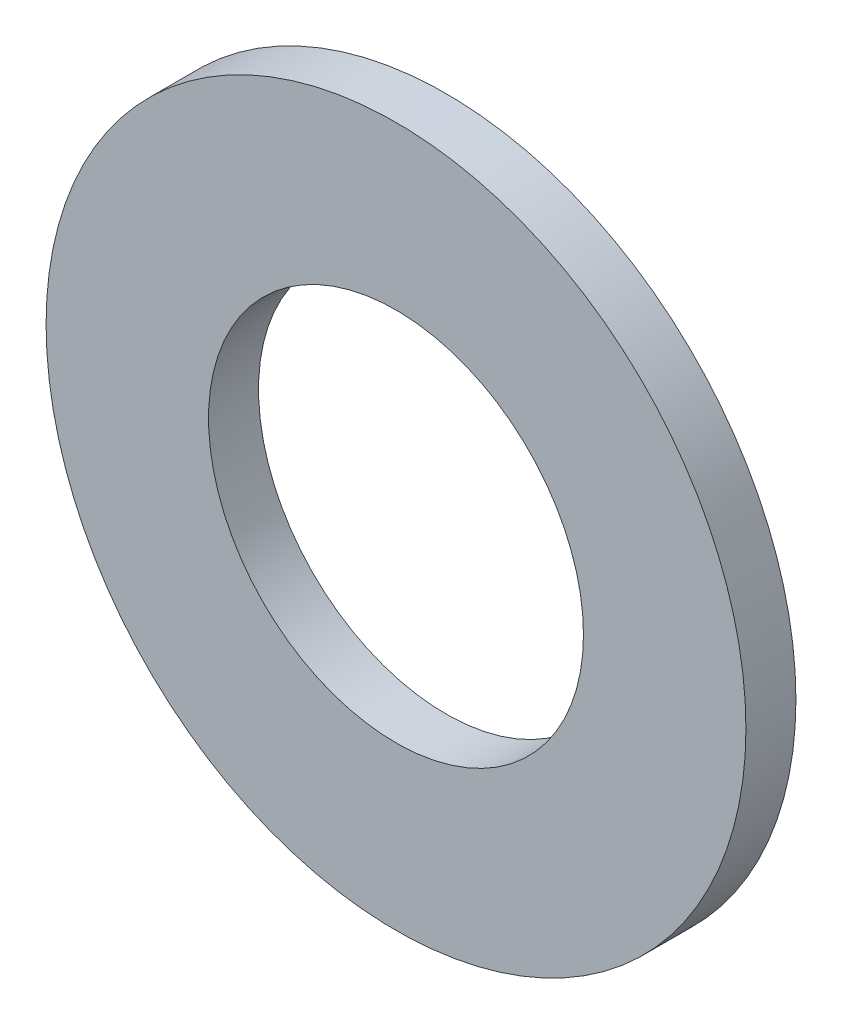
SolidWorks part; units mm, degrees
ref_plane "Front Plane" through (0, 0, 0) normal (0, 0, 1) x (1, 0, 0)
ref_plane "Top Plane" through (0, 0, 0) normal (0, 1, 0) x (1, 0, 0)
ref_plane "Right Plane" through (0, 0, 0) normal (1, 0, 0) x (0, 0, -1)
sketch "Sketch1" plane through (0, 0, 0) normal (0, 0, 1) x (1, 0, 0)
  circle A0 centre (0, 0) radius 7.5
  circle A1 centre (0, 0) radius 14
  dimension "D1" = 15
  dimension "D2" = 28
extrude "Boss-Extrude1" add sketch "Sketch1" along normal blind 2
